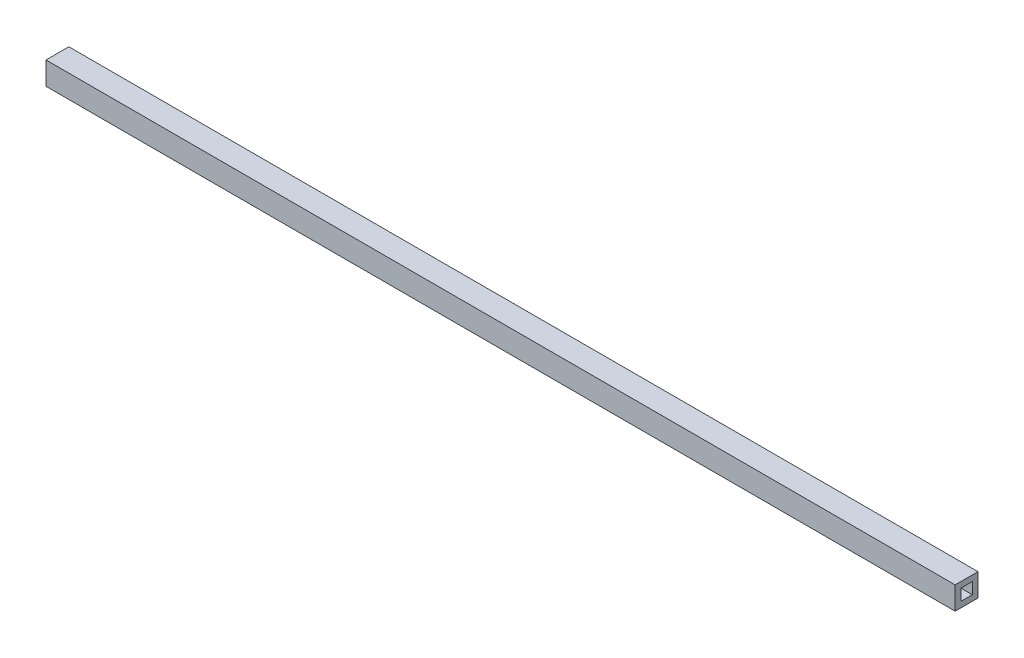
SolidWorks part; units mm, degrees
ref_plane "Front Plane" through (0, 0, 0) normal (0, 0, 1) x (1, 0, 0)
ref_plane "Top Plane" through (0, 0, 0) normal (0, 1, 0) x (1, 0, 0)
ref_plane "Right Plane" through (0, 0, 0) normal (1, 0, 0) x (0, 0, -1)
sketch "Sketch1" plane through (0, 0, 0) normal (1, 0, 0) x (0, 0, -1)
  line L1 (10, 10) -> (-10, 10)
  line L2 (-10, 10) -> (-10, -10)
  line L3 (-10, -10) -> (10, -10)
  line L4 (10, -10) -> (10, 10)
  circle A0 centre (0, 0) radius 10 construction
extrude "Boss-Extrude1" add sketch "Sketch1" along normal blind 796
sketch "Sketch3" plane through (796, 0, 0) normal (1, 0, 0) x (0, 0, -1)
  line L1 (5, 5) -> (-5, 5)
  line L2 (-5, 5) -> (-5, -5)
  line L3 (-5, -5) -> (5, -5)
  line L4 (5, -5) -> (5, 5)
  circle A0 centre (0, 0) radius 5 construction
extrude "Cut-Extrude1" cut sketch "Sketch3" against normal blind 10
sketch "Sketch4" plane through (0, 0, 0) normal (-1, 0, 0) x (0, 0, 1)
  line L1 (5, 5) -> (-5, 5)
  line L2 (-5, 5) -> (-5, -5)
  line L3 (-5, -5) -> (5, -5)
  line L4 (5, -5) -> (5, 5)
  circle A0 centre (0, 0) radius 5 construction
extrude "Cut-Extrude2" cut sketch "Sketch4" against normal blind 10
